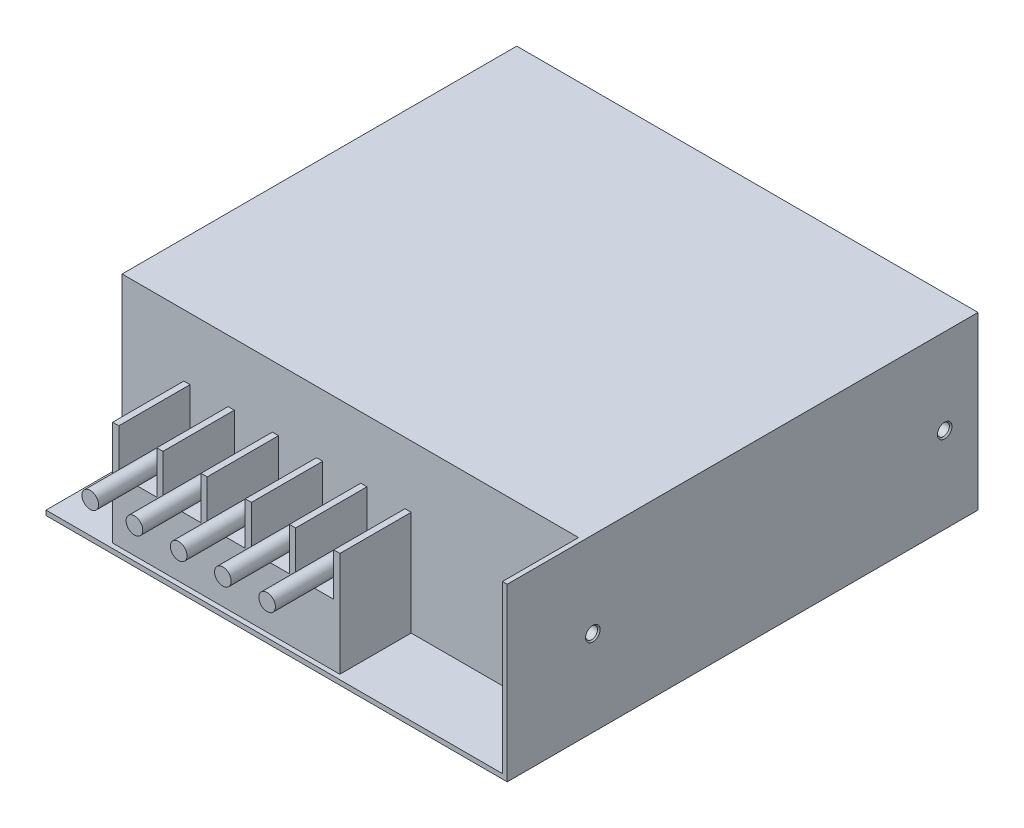
SolidWorks part; units mm, degrees
material "1023 Carbon Steel Sheet (SS)"
ref_plane "Front Plane" through (0, 0, 0) normal (0, 0, 1) x (1, 0, 0)
ref_plane "Top Plane" through (0, 0, 0) normal (0, 1, 0) x (1, 0, 0)
ref_plane "Right Plane" through (0, 0, 0) normal (1, 0, 0) x (0, 0, -1)
sketch "Sketch1" plane through (0, 0, 0) normal (0, 1, 0) x (1, 0, 0)
  line L1 (-48.5, 49.5) -> (48.5, 49.5)
  line L2 (-48.5, 49.5) -> (-48.5, -49.5)
  line L3 (-48.5, -49.5) -> (48.5, -49.5)
  line L4 (48.5, 49.5) -> (48.5, -49.5)
  point P4 (0, 49.5)
  point P6 (48.5, 0)
  dimension "D1" = 97
  dimension "D2" = 99
extrude "Boss-Extrude1" add sketch "Sketch1" along normal blind 36
sketch "Sketch2" plane through (0, 0, 49.5) normal (0, 0, 1) x (1, 0, 0)
  line L0 (48.5, 36) -> (48.5, 0) construction
  line L1 (-48.5, 36) -> (47.5, 36)
  line L2 (-48.5, 36) -> (-48.5, 1)
  line L3 (-48.5, 1) -> (47.5, 1)
  line L4 (47.5, 36) -> (47.5, 1)
  line L5 (-48.5, 0) -> (48.5, 0) construction
  dimension "D1" = 1
  dimension "D2" = 1
extrude "Cut-Extrude1" cut sketch "Sketch2" against normal blind 16
sketch "Sketch3" plane through (0, 0, 33.5) normal (0, 0, 1) x (1, 0, 0)
  line L0 (-48.5, 1) -> (47.5, 1) construction
  line L1 (-35.5, 1) -> (12.3, 1)
  line L2 (-35.5, 1) -> (-35.5, 23)
  line L3 (-35.5, 23) -> (-34.2, 23)
  line L4 (12.3, 1) -> (12.3, 23)
  line L5 (-48.5, 36) -> (-48.5, 1) construction
  line L6 (-26.2, 23) -> (-24.9, 23)
  line L8 (-34.2, 23) -> (-34.2, 14)
  line L9 (-34.2, 14) -> (-26.2, 14)
  line L10 (-26.2, 23) -> (-26.2, 14)
  line L12 (-24.9, 23) -> (-24.9, 14)
  line L13 (-24.9, 14) -> (-16.9, 14)
  line L14 (-16.9, 23) -> (-16.9, 14)
  line L16 (-15.6, 23) -> (-15.6, 14)
  line L17 (-15.6, 14) -> (-7.6, 14)
  line L18 (-7.6, 23) -> (-7.6, 14)
  line L20 (-6.3, 23) -> (-6.3, 14)
  line L21 (-6.3, 14) -> (1.7, 14)
  line L22 (1.7, 23) -> (1.7, 14)
  line L24 (3, 23) -> (3, 14)
  line L25 (3, 14) -> (11, 14)
  line L26 (11, 23) -> (11, 14)
  line L27 (-16.9, 23) -> (-15.6, 23)
  line L28 (-7.6, 23) -> (-6.3, 23)
  line L29 (1.7, 23) -> (3, 23)
  line L30 (11, 23) -> (12.3, 23)
  dimension "D1" = 13
  dimension "D2" = 47.8
  dimension "D3" = 22
  dimension "D4" = 8
  dimension "D5" = 13
extrude "Boss-Extrude2" add sketch "Sketch3" along normal blind 15
sketch "Sketch4" plane through (0, 0, 33.5) normal (0, 0, 1) x (1, 0, 0)
  line L0 (-26.2, 14) -> (-34.2, 14) construction
  line L1 (-16.9, 14) -> (-24.9, 14) construction
  line L2 (-7.6, 14) -> (-15.6, 14) construction
  line L3 (1.7, 14) -> (-6.3, 14) construction
  line L4 (11, 14) -> (3, 14) construction
  circle A0 centre (-30.2, 16.5) radius 1.75
  circle A1 centre (-20.9, 16.5) radius 1.75
  circle A2 centre (-11.6, 16.5) radius 1.75
  circle A3 centre (-2.3, 16.5) radius 1.75
  circle A4 centre (7, 16.5) radius 1.75
  point P12 (-30.2, 14)
  point P15 (-20.9, 14)
  point P18 (-11.6, 14)
  point P21 (-2.3, 14)
  point P24 (7, 14)
  dimension "D1" = 3.5
  dimension "D2" = 2.5
extrude "Boss-Extrude3" add sketch "Sketch4" along normal blind 25
sketch "Sketch5" plane through (48.5, 0, 0) normal (1, 0, 0) x (0, 0, -1)
  line L0 (42.5, 18) -> (-31.5, 18) construction
  line L1 (-49.5, 0) -> (49.5, 0) construction
  line L2 (-49.5, 36) -> (-49.5, 0) construction
  dimension "D1" = 74
  dimension "D2" = 18
  dimension "D3" = 18
hole_wizard "M3 Tapped Hole1" positions "Sketch7" profile "Sketch6" tap size "M3" standard "DIN"
sketch "Sketch7" plane through (48.5, 0, 0) normal (1, 0, 0) x (0, 0, -1)
  point P0 (-31.5, 18)
  point P3 (42.5, 18)
sketch "Sketch6" plane through (48.5, 18, 31.5) normal (0, 1, 0) x (0, 0, -1)
  line L0 (0, 0) -> (0, 5.2511)
  line L1 (0, 5.2511) -> (1.25, 4.5)
  line L2 (1.25, 4.5) -> (1.25, 0.275)
  line L3 (1.25, 0.275) -> (1.525, 0)
  line L5 (1.525, 0) -> (0, 0)
  line L6 (-1.25, 0.275) -> (-1.525, 0) construction
  line L10 (0, 5.2511) -> (-1.25, 4.5) construction
  line L11 (0, -6.35) -> (0, 107.95) construction
  dimension "Tap Drill Dia." = 2.5
  dimension "Tap Drill Depth" = 4.5
  dimension "Near C'Sink Dia." = 3.05
  dimension "Near C'Sink Angle" = 90
  dimension "Drill Angle" = 118
cosmetic thread "Hole Thread1" parameters "D1"=4.5, "D2"=3
cosmetic thread "Hole Thread2" parameters "D1"=4.5, "D2"=3
sketch "Sketch8" plane through (0, 0, 0) normal (0, -1, 0) x (1, 0, 0)
  line L0 (3, -26) -> (3, 29)
  line L1 (-48.5, 49.5) -> (48.5, 49.5) construction
  line L2 (-48.5, -49.5) -> (-48.5, 49.5) construction
  dimension "D1" = 55
  dimension "D2" = 20.5
  dimension "D3" = 51.5
hole_wizard "M3 Tapped Hole2" positions "Sketch10" profile "Sketch9" tap size "M3" standard "DIN"
sketch "Sketch10" plane through (0, 0, 0) normal (0, -1, 0) x (-1, 0, 0)
  point P0 (-3, -29)
  point P3 (-3, 26)
sketch "Sketch9" plane through (3, 0, 29) normal (1, 0, 0) x (0, 0, -1)
  line L0 (0, 0) -> (0, 5.2511)
  line L1 (0, 5.2511) -> (1.25, 4.5)
  line L2 (1.25, 4.5) -> (1.25, 0.275)
  line L3 (1.25, 0.275) -> (1.525, 0)
  line L5 (1.525, 0) -> (0, 0)
  line L6 (-1.25, 0.275) -> (-1.525, 0) construction
  line L10 (0, 5.2511) -> (-1.25, 4.5) construction
  line L11 (0, -6.35) -> (0, 107.95) construction
  dimension "Tap Drill Dia." = 2.5
  dimension "Tap Drill Depth" = 4.5
  dimension "Near C'Sink Dia." = 3.05
  dimension "Near C'Sink Angle" = 90
  dimension "Drill Angle" = 118
cosmetic thread "Hole Thread3" parameters "D1"=4.5, "D2"=3
cosmetic thread "Hole Thread4" parameters "D1"=4.5, "D2"=3
